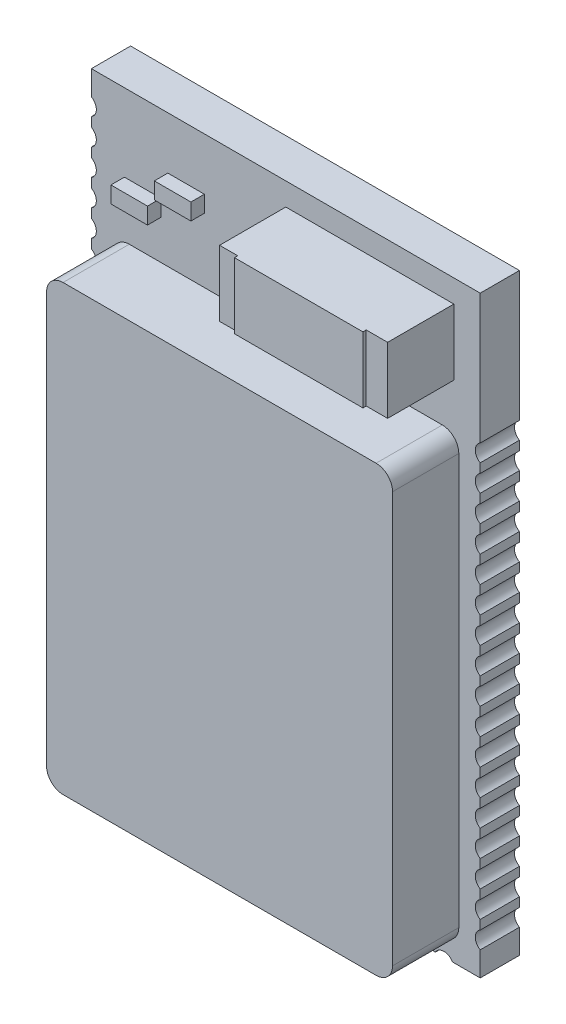
SolidWorks part; units mm, degrees
ref_plane "Front Plane" through (0, 0, 0) normal (0, 0, 1) x (1, 0, 0)
ref_plane "Top Plane" through (0, 0, 0) normal (0, 1, 0) x (1, 0, 0)
ref_plane "Right Plane" through (0, 0, 0) normal (1, 0, 0) x (0, 0, -1)
sketch "Sketch1" plane through (0, 0, 0) normal (0, 0, 1) x (1, 0, 0)
  line L1 (0, 0) -> (11.8, 0)
  line L2 (0, 0) -> (0, 18)
  line L3 (0, 18) -> (11.8, 18)
  line L4 (11.8, 0) -> (11.8, 18)
  dimension "D1" = 11.8
  dimension "D2" = 18
extrude "Boss-Extrude1" add sketch "Sketch1" along normal blind 1.19
sketch "Sketch2" plane through (0, 0, 0) normal (0, 0, 1) x (1, 0, 0)
  line L1 (0.65, 0.5) -> (11.15, 0.5)
  line L2 (0.65, 0.5) -> (0.65, 13.96)
  line L3 (0.65, 13.96) -> (11.15, 13.96)
  line L4 (11.15, 0.5) -> (11.15, 13.96)
extrude "Boss-Extrude2" add sketch "Sketch2" along normal blind 3.2
fillet "Fillet11" radius 0.5 1 edges at (0.65, 13.96, 2.195)
fillet "Fillet12" radius 0.5 1 edges at (0.65, 0.5, 2.195)
fillet "Fillet13" radius 0.5 1 edges at (11.15, 0.5, 2.195)
fillet "Fillet14" radius 0.5 1 edges at (11.15, 13.96, 2.195)
sketch "Sketch9" plane through (0, 0, 0) normal (0, 0, 1) x (1, 0, 0)
  circle A0 centre (1.1, -0.15) radius 0.3
  circle A1 centre (1.9, -0.15) radius 0.3
  circle A2 centre (2.7, -0.15) radius 0.3
  circle A3 centre (3.5, -0.15) radius 0.3
  circle A4 centre (4.3, -0.15) radius 0.3
  circle A5 centre (5.1, -0.15) radius 0.3
  circle A6 centre (5.9, -0.15) radius 0.3
  circle A7 centre (6.7, -0.15) radius 0.3
  circle A8 centre (7.5, -0.15) radius 0.3
  circle A9 centre (8.3, -0.15) radius 0.3
  circle A10 centre (9.1, -0.15) radius 0.3
  circle A11 centre (9.9, -0.15) radius 0.3
  circle A12 centre (10.7, -0.15) radius 0.3
  dimension "D1" = 13
extrude "Cut-Extrude5" cut sketch "Sketch9" along direction (0, 0, -1) on the side of the normal blind 3.2
sketch "Sketch14" plane through (0, 0, 0) normal (0, 0, 1) x (1, 0, 0)
  line L1 (5.9, 15.3127) -> (11, 15.3127)
  line L2 (5.9, 15.3127) -> (5.9, 17.3127)
  line L3 (5.9, 17.3127) -> (11, 17.3127)
  line L4 (11, 15.3127) -> (11, 17.3127)
extrude "Boss-Extrude3" add sketch "Sketch14" along normal blind 3.2
sketch "Sketch15" plane through (0, 0, 0) normal (0, 0, 1) x (1, 0, 0)
  line L0 (5.9, 15.3127) -> (11, 15.3127) construction
  line L1 (6.451, 15.3127) -> (10.351, 15.3127)
  line L2 (6.451, 15.3127) -> (6.451, 17.3127)
  line L3 (6.451, 17.3127) -> (10.351, 17.3127)
  line L4 (10.351, 15.3127) -> (10.351, 17.3127)
  line L5 (11, 17.3127) -> (5.9, 17.3127) construction
  dimension "D1" = 3.9
extrude "Boss-Extrude4" add sketch "Sketch15" along normal blind 3.3
sketch "Sketch16" plane through (0, 0, 0) normal (0, 0, 1) x (1, 0, 0)
  circle A0 centre (-0.15, 1) radius 0.3
  circle A1 centre (-0.15, 1.8) radius 0.3
  circle A2 centre (-0.15, 2.6) radius 0.3
  circle A3 centre (-0.15, 3.4) radius 0.3
  circle A4 centre (-0.15, 4.2) radius 0.3
  circle A5 centre (-0.15, 5) radius 0.3
  circle A6 centre (-0.15, 5.8) radius 0.3
  circle A7 centre (-0.15, 6.6) radius 0.3
  circle A8 centre (-0.15, 7.4) radius 0.3
  circle A9 centre (-0.15, 8.2) radius 0.3
  circle A10 centre (-0.15, 9) radius 0.3
  circle A11 centre (-0.15, 9.8) radius 0.3
  circle A12 centre (-0.15, 10.6) radius 0.3
  circle A13 centre (-0.15, 11.4) radius 0.3
  circle A14 centre (-0.15, 12.2) radius 0.3
  circle A15 centre (-0.15, 13) radius 0.3
  circle A16 centre (-0.15, 13.8) radius 0.3
  circle A17 centre (-0.15, 14.6) radius 0.3
  circle A18 centre (-0.15, 15.4) radius 0.3
  circle A19 centre (-0.15, 16.2) radius 0.3
  circle A20 centre (-0.15, 17) radius 0.3
  dimension "D1" = 21
extrude "Cut-Extrude6" cut sketch "Sketch16" along normal through all both and the other way through all
sketch "Sketch17" plane through (0, 0, 0) normal (0, 0, 1) x (1, 0, 0)
  circle A0 centre (11.95, 1) radius 0.3
  circle A1 centre (11.95, 1.8) radius 0.3
  circle A2 centre (11.95, 2.6) radius 0.3
  circle A3 centre (11.95, 3.4) radius 0.3
  circle A4 centre (11.95, 4.2) radius 0.3
  circle A5 centre (11.95, 5) radius 0.3
  circle A6 centre (11.95, 5.8) radius 0.3
  circle A7 centre (11.95, 6.6) radius 0.3
  circle A8 centre (11.95, 7.4) radius 0.3
  circle A9 centre (11.95, 8.2) radius 0.3
  circle A10 centre (11.95, 9) radius 0.3
  circle A11 centre (11.95, 9.8) radius 0.3
  circle A12 centre (11.95, 10.6) radius 0.3
  circle A13 centre (11.95, 11.4) radius 0.3
  circle A14 centre (11.95, 12.2) radius 0.3
  circle A15 centre (11.95, 13) radius 0.3
  circle A16 centre (11.95, 13.8) radius 0.3
  dimension "D1" = 17
extrude "Cut-Extrude9" cut sketch "Sketch17" against normal blind 3.2 and the other way through all
sketch "Sketch19" plane through (0, 0, 0) normal (0, 0, 1) x (1, 0, 0)
  line L1 (2.32, 15.9147) -> (3.43, 15.9147)
  line L2 (2.32, 15.9147) -> (2.32, 16.4147)
  line L3 (2.32, 16.4147) -> (3.43, 16.4147)
  line L4 (3.43, 15.9147) -> (3.43, 16.4147)
  dimension "D1" = 1.11
  dimension "D2" = 0.5
extrude "Boss-Extrude6" add sketch "Sketch19" along normal blind 1.6
sketch "Sketch20" plane through (0, 0, 0) normal (0, 0, 1) x (1, 0, 0)
  line L1 (2.1127, 15.6494) -> (1.0027, 15.6494)
  line L2 (2.1127, 15.6494) -> (2.1127, 15.1494)
  line L3 (2.1127, 15.1494) -> (1.0027, 15.1494)
  line L4 (1.0027, 15.6494) -> (1.0027, 15.1494)
  dimension "D1" = 1.11
  dimension "D2" = 0.5
extrude "Boss-Extrude7" add sketch "Sketch20" along normal blind 1.6
